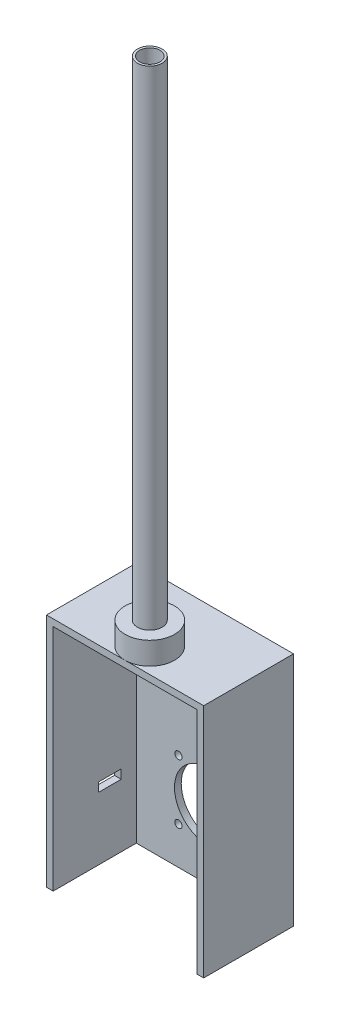
SolidWorks part; units mm, degrees
ref_plane "前视基准面" through (0, 0, 0) normal (0, 0, 1) x (1, 0, 0)
ref_plane "上视基准面" through (0, 0, 0) normal (0, 1, 0) x (1, 0, 0)
ref_plane "右视基准面" through (0, 0, 0) normal (1, 0, 0) x (0, 0, -1)
sketch "草图1" plane through (0, 0, 0) normal (0, 1, 0) x (1, 0, 0)
  circle A0 centre (0, 0) radius 22
  dimension "D1" = 44
extrude "凸台-拉伸1" add sketch "草图1" along normal blind 20
sketch "草图2" plane through (0, 20, 0) normal (0, 1, 0) x (1, 0, 0)
  circle A0 centre (0, 0) radius 11
  dimension "D1" = 22
extrude "凸台-拉伸2" add sketch "草图2" along normal blind 435
sketch "草图3" plane through (0, 455, 0) normal (0, 1, 0) x (1, 0, 0)
  circle A0 centre (0, 0) radius 8
  dimension "D1" = 16
sketch "草图4" plane through (0, 0, 0) normal (0, -1, 0) x (1, 0, 0)
  line L1 (-70, 22) -> (70, 22)
  line L2 (-70, 22) -> (-70, -58)
  line L3 (-70, -58) -> (70, -58)
  line L4 (70, 22) -> (70, -58)
  line L5 (-70, 22) -> (70, -58) construction
  line L6 (-70, -58) -> (70, 22) construction
  circle A1 centre (0, 0) radius 22 construction
  point P8 (0, -18)
  dimension "D1" = 140
  dimension "D2" = 80
extrude "凸台-拉伸3" add sketch "草图4" along normal blind 210 separate body
shell "抽壳2" thickness 6
extrude "切除-拉伸2" cut sketch "草图3" against normal up to surface (461 mm away) contours A0 up to face at (0, -6, -15)
sketch "草图5" plane through (0, 0, 22) normal (0, 0, 1) x (1, 0, 0)
  line L0 (70, -210) -> (-70, -210) construction
  line L1 (64, -204) -> (-64, -204)
  line L2 (64, -204) -> (64, -210)
  line L3 (64, -210) -> (-64, -210)
  line L4 (-64, -204) -> (-64, -210)
  line L5 (-64, -204) -> (-64, -6) construction
extrude "切除-拉伸3" cut sketch "草图5" against normal up to surface (74 mm away) up to face at (0, -105, -52)
sketch "草图6" plane through (0, 0, -58) normal (0, 0, -1) x (-1, 0, 0)
  line L1 (0, -150) -> (82.393, -67.607) construction
  circle A0 centre (0, -150) radius 30
  circle A1 centre (26.5165, -123.4835) radius 3.25
  circle A2 centre (26.5165, -176.5165) radius 3.25
  circle A3 centre (-26.5165, -176.5165) radius 3.25
  circle A4 centre (-26.5165, -123.4835) radius 3.25
  point P21 (0, -150)
  dimension "D1" = 60
  dimension "D5" = 6.5
  dimension "D2" = 150
  dimension "D4" = 37.5
  dimension "D6" = 4
extrude "切除-拉伸4" cut sketch "草图6" against normal blind 10
sketch "草图7" plane through (0, 455, 0) normal (0, 1, 0) x (1, 0, 0)
  circle A0 centre (0, 0) radius 9
  dimension "D1" = 18
extrude "切除-拉伸5" cut sketch "草图7" against normal blind 18
sketch "草图8" plane through (0, -6, 0) normal (0, -1, 0) x (1, 0, 0)
  circle A0 centre (0, 0) radius 9
  dimension "D1" = 18
extrude "切除-拉伸6" cut sketch "草图8" against normal blind 18
sketch "草图9" plane through (-70, 0, 0) normal (-1, 0, 0) x (0, 0, 1)
  line L0 (-58, -120) -> (-58, -180) construction
  line L1 (-18.5, -146) -> (-38.5, -146)
  line L2 (-18.5, -146) -> (-18.5, -154)
  line L3 (-18.5, -154) -> (-38.5, -154)
  line L4 (-38.5, -146) -> (-38.5, -154)
  line L5 (-18.5, -146) -> (-38.5, -154) construction
  line L6 (-18.5, -154) -> (-38.5, -146) construction
  line L7 (-58, -120) -> (-58, -180) construction
  point P0 (-28.5, -150)
  point P5 (0, 0)
  point P8 (-58, -150)
  dimension "D1" = 20
  dimension "D2" = 8
  dimension "D3" = 39
extrude "切除-拉伸7" cut sketch "草图9" against normal blind 10
